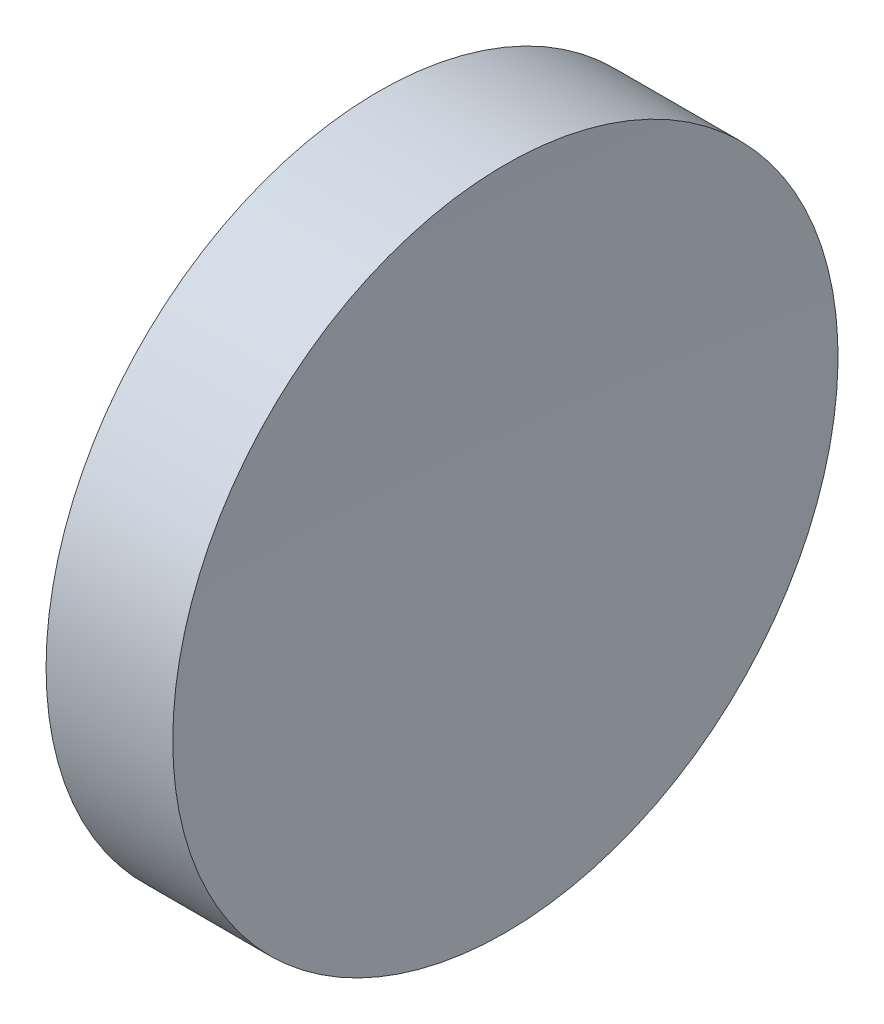
SolidWorks part; units mm, degrees
ref_plane "前视基准面" through (0, 0, 0) normal (0, 0, 1) x (1, 0, 0)
ref_plane "上视基准面" through (0, 0, 0) normal (0, 1, 0) x (1, 0, 0)
ref_plane "右视基准面" through (0, 0, 0) normal (1, 0, 0) x (0, 0, -1)
sketch "草图1" plane through (0, 0, 0) normal (0, 0, 1) x (1, 0, 0)
  line L0 (217.9703, 138.756) -> (265.5527, 138.756) construction
  line L1 (230.1853, 138.756) -> (230.1853, 163.756)
  line L2 (239.1853, 138.756) -> (230.1853, 138.756)
  line L3 (230.1853, 163.756) -> (239.7064, 163.756)
  arc A0 (239.7064, 163.756) -> (239.1853, 138.756) centre (839.1853, 138.756) ccw
  dimension "D2" = 600
  dimension "D1" = 9.5211
revolve "旋转1" add sketch "草图1" angle 360 about L0
